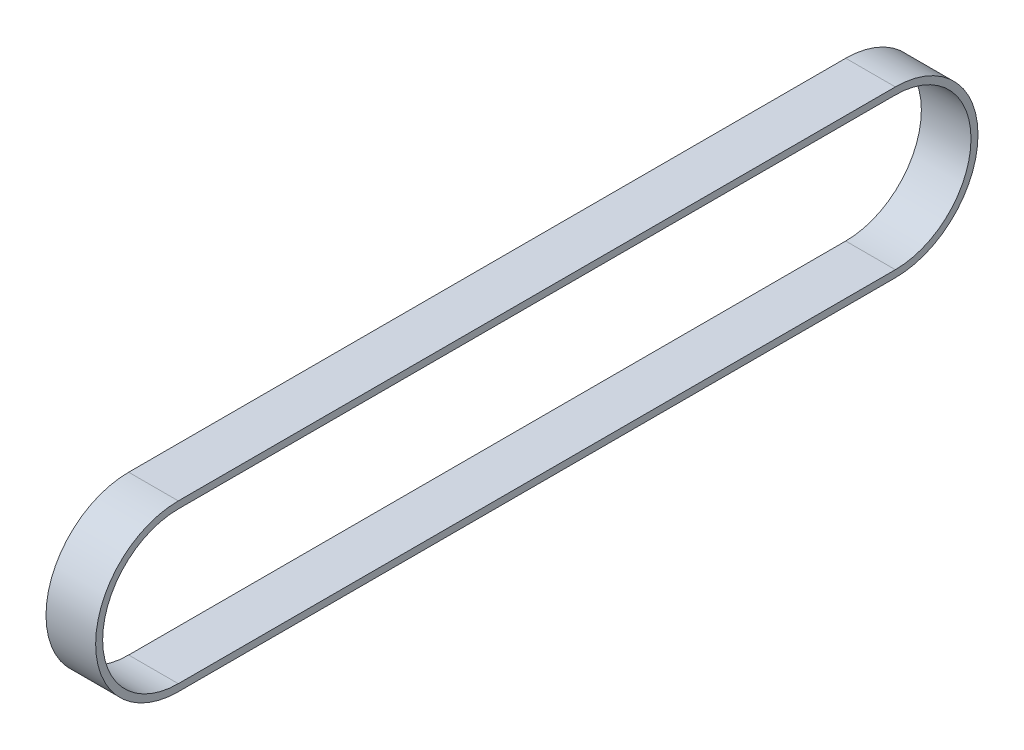
SolidWorks part; units mm, degrees
ref_plane "Front Plane" through (0, 0, 0) normal (0, 0, 1) x (1, 0, 0)
ref_plane "Top Plane" through (0, 0, 0) normal (0, 1, 0) x (1, 0, 0)
ref_plane "Right Plane" through (0, 0, 0) normal (1, 0, 0) x (0, 0, -1)
sketch "Sketch1" plane through (0, 0, 0) normal (1, 0, 0) x (0, 0, -1)
  line L0 (0, 0) -> (130, 0) construction
  line L1 (0, 13.716) -> (130, 13.716)
  line L2 (130, -13.716) -> (0, -13.716)
  arc A0 (0, 13.716) -> (0, -13.716) centre (0, 0) ccw
  arc A1 (130, -13.716) -> (130, 13.716) centre (130, 0) ccw
  dimension "D2" = 27.432
  dimension "D1" = 130
extrude "Extrude-Thin1" add sketch "Sketch1" along normal blind 9 thin thin type one direction wall 1.27
